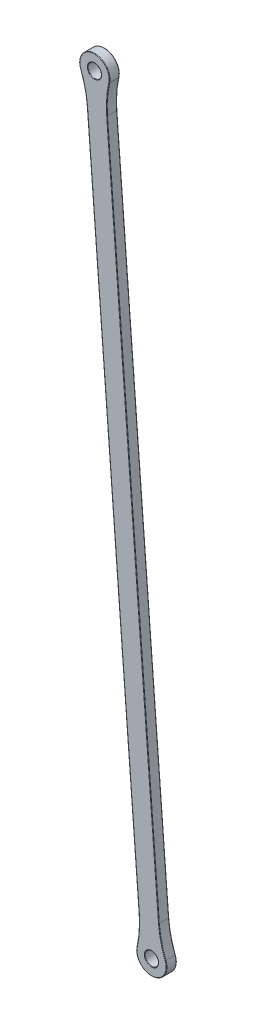
SolidWorks part; units mm, degrees
ref_plane "Front Plane" through (0, 0, 0) normal (0, 0, 1) x (1, 0, 0)
ref_plane "Top Plane" through (0, 0, 0) normal (0, 1, 0) x (1, 0, 0)
ref_plane "Right Plane" through (0, 0, 0) normal (1, 0, 0) x (0, 0, -1)
sketch "Sketch1" plane through (0, 0, 0) normal (0, 0, 1) x (1, 0, 0)
  line L0 (14.5, 81.5) -> (-2.5448, 302.8447) construction
  line L1 (14.5, 81.5) -> (-2.5448, 302.8447) construction
  line L2 (-2.5448, 302.8447) -> (14.5, 81.5) construction
  line L3 (0.4464, 303.075) -> (17.4911, 81.7303)
  line L4 (-5.5359, 302.6144) -> (11.5089, 81.2697)
  circle A0 centre (-2.5448, 302.8447) radius 4.5 construction
  circle A1 centre (14.5, 81.5) radius 4.5 construction
  arc A2 (0.4464, 303.075) -> (-5.5359, 302.6144) centre (-2.5448, 302.8447) ccw
  arc A3 (11.5089, 81.2697) -> (17.4911, 81.7303) centre (14.5, 81.5) ccw
  arc A4 (17.4911, 81.7303) -> (11.5089, 81.2697) centre (14.5, 81.5) ccw
  arc A5 (0.4464, 303.075) -> (-5.5359, 302.6144) centre (-2.5448, 302.8447) cw
  arc A6 (17.2336, 85.0745) -> (11.2513, 84.6139) centre (14.5, 81.5) cw
  arc A7 (0.7039, 299.7308) -> (-5.2784, 299.2702) centre (-2.5448, 302.8447) ccw
  circle A8 centre (-2.5448, 302.8447) radius 2
  circle A9 centre (14.5, 81.5) radius 2
  point P4 (5.9776, 192.1723)
  dimension "D1" = 9
  dimension "D3" = 4
  dimension "D4" = 4
  dimension "D2" = 6
extrude "Boss-Extrude1" add sketch "Sketch1" against normal blind 3 contours A6 L3 A3 L4 | L3 A5 L4 A4 | L3 A7 L4 A2 | A5 A2 A8 | A3 A4 A9
fillet "Fillet1" radius 30 4 edges at (11.2513, 84.6139, -1.5) (17.2336, 85.0745, -1.5) (-5.2784, 299.2702, -1.5) (0.7039, 299.7308, -1.5)
fillet "Fillet2" radius 0.15 20 edges at (-5.4299, 296.9668, -3) (-5.4299, 296.9668, 0) (2.9865, 191.942, -3) (2.9865, 191.942, 0) (10.749, 86.8669, -3) (10.749, 86.8669, 0) (14.8455, 77.0133, 0) (14.8455, 77.0133, -3) (17.3851, 87.3779, -3) (17.3851, 87.3779, 0) (8.9688, 192.4027, 0) (8.9688, 192.4027, -3) (1.2062, 297.4778, -3) (1.2062, 297.4778, 0) (-2.8903, 307.3314, -3) (-2.8903, 307.3314, 0) (-0.5448, 302.8447, -3) (-0.5448, 302.8447, 0) (16.5, 81.5, -3) (16.5, 81.5, 0)
